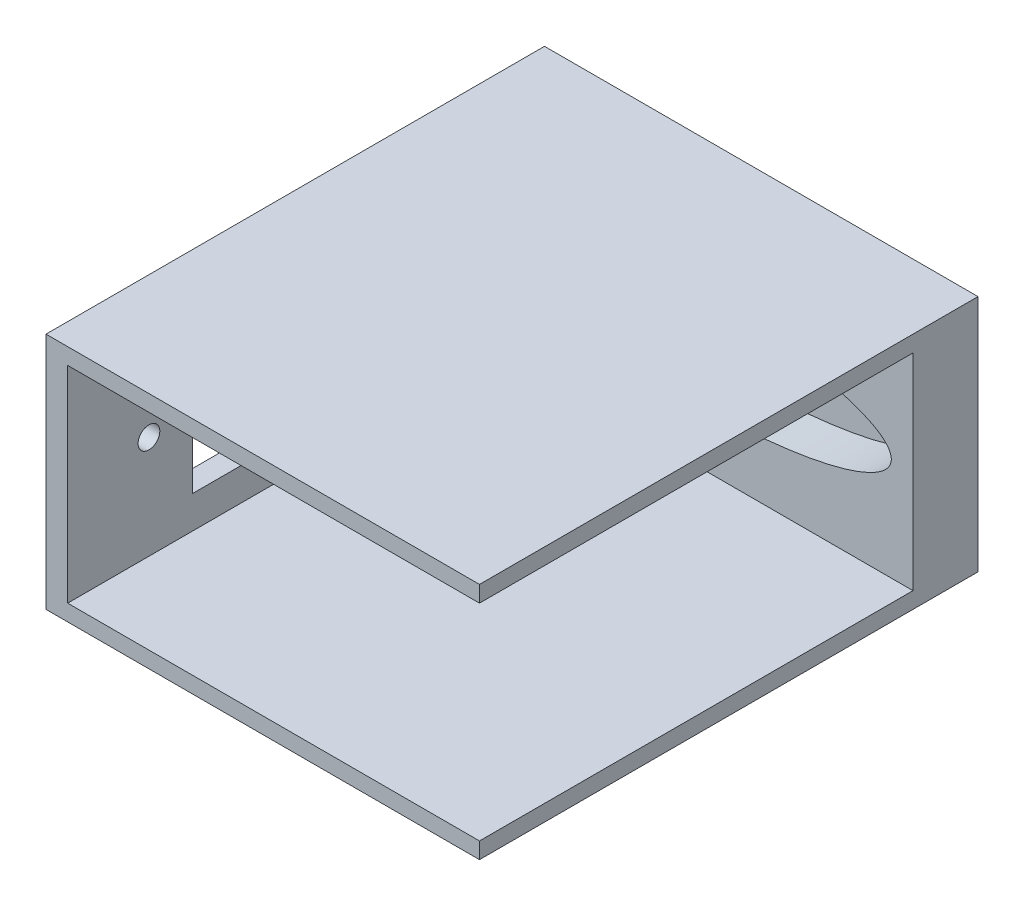
SolidWorks part; units mm, degrees
ref_plane "前视基准面" through (0, 0, 0) normal (0, 0, 1) x (1, 0, 0)
ref_plane "上视基准面" through (0, 0, 0) normal (0, 1, 0) x (1, 0, 0)
ref_plane "右视基准面" through (0, 0, 0) normal (1, 0, 0) x (0, 0, -1)
sketch "草图1" plane through (0, 0, 0) normal (0, 0, 1) x (1, 0, 0)
  line L0 (0, 0) -> (18, 0) construction
  line L1 (0, 0) -> (0, 9.5) construction
  line L3 (-20, -11) -> (20, -11)
  line L4 (-20, -11) -> (-20, 11)
  line L5 (-20, 11) -> (20, 11)
  line L6 (20, -11) -> (20, 11)
  line L7 (-20, -11) -> (20, 11) construction
  line L8 (-20, 11) -> (20, -11) construction
  circle A0 centre (0, 0) radius 4.5
  ellipse E0 centre (0, 0) end of major axis (18, 0) minor radius 4.5 (-3.9912, 4.388) -> (-3.9912, -4.388) ccw
  ellipse E1 centre (0, 0) end of major axis (0, 9.5) minor radius 4.5 (-3.9912, -4.388) -> (3.9912, -4.388) ccw
  ellipse E2 centre (0, 0) end of major axis (0, 9.5) minor radius 4.5 (3.9912, 4.388) -> (-3.9912, 4.388) ccw
  ellipse E3 centre (0, 0) end of major axis (18, 0) minor radius 4.5 (3.9912, -4.388) -> (3.9912, 4.388) ccw
  dimension "D1" = 9
  dimension "D2" = 40
  dimension "D3" = 22
extrude "凸台-拉伸1" add sketch "草图1" along normal blind 6 contours L3 L6 L5 L4 E3 E1 E0 E2 | E1 E3 E2 E0 A0 | A0
ref_plane "基准面1" through (0, 0, 6) normal (0, 0, 1) x (1, 0, 0)
sketch "草图3" plane through (0, 0, 6) normal (0, 0, 1) x (1, 0, 0)
  ellipse E0 centre (0, 0) end of major axis (18, 0) minor radius 4.5 (3.9912, -4.388) -> (3.9912, 4.388) ccw
  ellipse E1 centre (0, 0) end of major axis (0, 9.5) minor radius 4.5 (-3.9912, -4.388) -> (3.9912, -4.388) ccw
  ellipse E2 centre (0, 0) end of major axis (0, 9.5) minor radius 4.5 (3.9912, 4.388) -> (-3.9912, 4.388) ccw
  ellipse E3 centre (0, 0) end of major axis (18, 0) minor radius 4.5 (-3.9912, 4.388) -> (-3.9912, -4.388) ccw
extrude "切除-拉伸2" cut sketch "草图3" against normal blind 4
sketch "草图4" plane through (0, 0, 6) normal (0, 0, 1) x (1, 0, 0)
  circle A0 centre (0, 0) radius 4.5
extrude "切除-拉伸3" cut sketch "草图4" against normal through all contours A0
sketch "草图5" plane through (0, 0, 6) normal (0, 0, 1) x (1, 0, 0)
  line L0 (-20, -11) -> (-20, 11) construction
  line L1 (20, -11) -> (-20, -11)
  line L2 (20, -11) -> (20, -9.5)
  line L3 (20, -9.5) -> (-18, -9.5)
  line L4 (-20, -11) -> (-20, -9.5)
  line L6 (20, 11) -> (-20, 11)
  line L7 (20, 11) -> (20, 9.5)
  line L8 (20, 9.5) -> (-18, 9.5)
  line L9 (-20, 11) -> (-20, 9.5)
  line L11 (-20, -9.5) -> (-20, 9.5)
  line L13 (-18, -9.5) -> (-18, 9.5)
  ellipse E0 centre (0, 0) end of major axis (0, 9.5) minor radius 4.5 (-3.9912, -4.388) -> (3.9912, -4.388) ccw construction
  ellipse E1 centre (0, 0) end of major axis (0, 9.5) minor radius 4.5 (3.9912, 4.388) -> (-3.9912, 4.388) ccw construction
  ellipse E2 centre (0, 0) end of major axis (18, 0) minor radius 4.5 (-3.9912, 4.388) -> (-3.9912, -4.388) ccw construction
extrude "凸台-拉伸2" add sketch "草图5" along normal blind 40 contours L9 L11 L4 L1 L2 L3 L13 L8 L7 L6
ref_plane "基准面2" through (-20, 0, 0) normal (-1, 0, 0) x (0, 0, 1)
sketch "草图6" plane through (-20, 0, 0) normal (-1, 0, 0) x (0, 0, 1)
  line L0 (0, 0) -> (46, 0) construction
  line L1 (46, 11) -> (46, -11) construction
  line L2 (23, -11) -> (23, 11) construction
  line L3 (46, -11) -> (0, -11) construction
  line L4 (46, 11) -> (0, 11) construction
  line L6 (39.5, 6.5) -> (6.5, 6.5)
  line L7 (39.5, 6.5) -> (39.5, -6.5)
  line L8 (39.5, -6.5) -> (6.5, -6.5)
  line L9 (6.5, 6.5) -> (6.5, -6.5)
  line L10 (39.5, 6.5) -> (6.5, -6.5) construction
  line L11 (39.5, -6.5) -> (6.5, 6.5) construction
  line L12 (34.5, 6.5) -> (11.5, 6.5)
  line L13 (34.5, 6.5) -> (34.5, -6.5)
  line L14 (34.5, -6.5) -> (11.5, -6.5)
  line L15 (11.5, 6.5) -> (11.5, -6.5)
  line L16 (34.5, 6.5) -> (11.5, -6.5) construction
  line L17 (34.5, -6.5) -> (11.5, 6.5) construction
  point P11 (23, 0)
  point P16 (23, 0)
  dimension "D1" = 33
  dimension "D2" = 13
  dimension "D3" = 23
extrude "切除-拉伸4" cut sketch "草图6" against normal blind 40 contours L6 L15 L8 L13
sketch "草图7" plane through (-20, 0, 0) normal (-1, 0, 0) x (0, 0, 1)
  line L0 (39.5, -6.5) -> (39.5, 6.5) construction
  line L1 (39.5, 0) -> (38.5, 0) construction
  line L2 (0, 0) -> (46, 0) construction
  line L3 (23, 6.5) -> (23, -6.5) construction
  line L4 (39.5, 6.5) -> (6.5, 6.5) construction
  line L5 (39.5, -6.5) -> (6.5, -6.5) construction
  circle A0 centre (38.5, 0) radius 1
  circle A1 centre (7.5, 0) radius 1
extrude "切除-拉伸5" cut sketch "草图7" against normal blind 40
